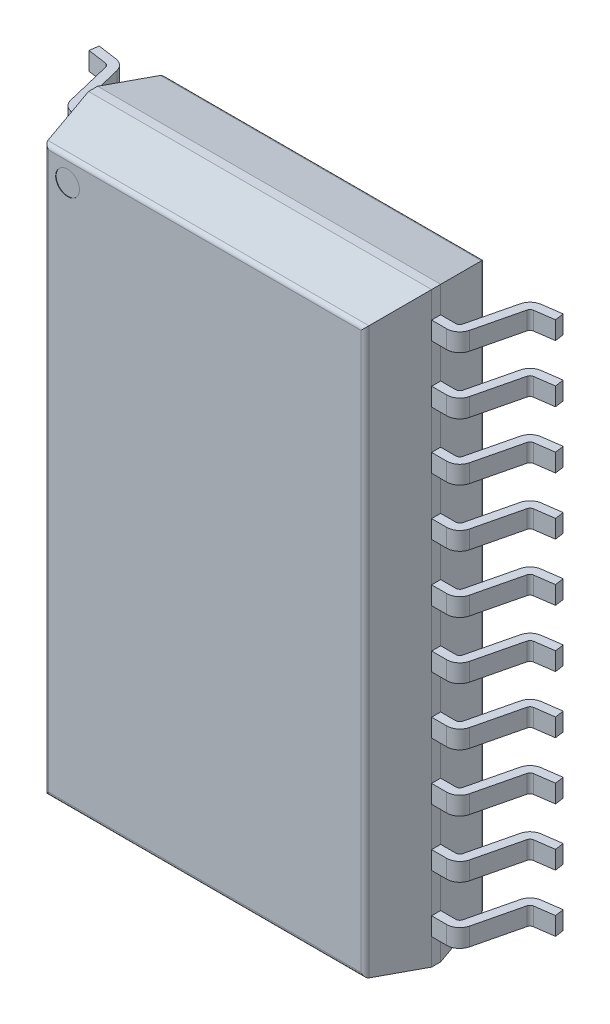
SolidWorks part; units mm, degrees
ref_plane "Front Plane" through (0, 0, 0) normal (0, 0, 1) x (1, 0, 0)
ref_plane "Top Plane" through (0, 0, 0) normal (0, 1, 0) x (1, 0, 0)
ref_plane "Right Plane" through (0, 0, 0) normal (1, 0, 0) x (0, 0, -1)
ref_plane "Body Standoff" through (0, 0.15, 0) normal (0, 1, 0) x (-1, 0, 0)
sketch "Sketch1" plane through (0, 0.15, 0) normal (0, 1, 0) x (-1, 0, 0)
  line L1 (3.8, 6.5) -> (-3.8, 6.5)
  line L2 (3.8, 6.5) -> (3.8, -6.5)
  line L3 (3.8, -6.5) -> (-3.8, -6.5)
  line L4 (-3.8, 6.5) -> (-3.8, -6.5)
  line L8 (0, 0) -> (0, -6.5) construction
  line L9 (0, 0) -> (-3.8, 0) construction
  dimension "D" = 13
  dimension "E1" = 7.6
extrude "Body" add sketch "Sketch1" along normal blind 2.65
chamfer "Body Chamfer" distance 1.225 angle 12 8 edges at (-3.8, 2.8, 0) (0, 0.15, 6.5) (3.8, 0.15, 0) (0, 0.15, -6.5) (-3.8, 0.15, 0) (0, 2.8, -6.5) (3.8, 2.8, 0) (0, 2.8, 6.5)
fillet "Fillet1" radius 0.1 8 edges at (0, 0.15, -6.2396) (-3.5396, 0.15, 0) (0, 0.15, 6.2396) (3.5396, 0.15, 0) (0, 2.8, 6.2396) (-3.5396, 2.8, 0) (0, 2.8, -6.2396) (3.5396, 2.8, 0)
sketch "Sketch2" plane through (0, 2.8, 0) normal (0, 1, 0) x (1, 0, 0)
  line L0 (3.5396, 6.2396) -> (-3.5396, 6.2396) construction
  line L1 (-3.5396, 6.2396) -> (-3.5396, -6.2396) construction
  circle A0 centre (-3.0396, 5.7396) radius 0.2635
  dimension "D1" = 0.5
  dimension "D2" = 0.5
extrude "Pin #1 Indent" cut sketch "Sketch2" against normal blind 0.01
ref_plane "Pin Offset" through (0, 0, 0.635) normal (0, 0, 1) x (1, 0, 0)
sketch "Sketch3" plane through (0, 0, 0.635) normal (0, 0, 1) x (1, 0, 0)
  line L0 (-5.14, 0) -> (-4.7116, 0.0602)
  line L2 (0, 0) -> (-5.14, 0) construction
  line L3 (-5.14, 0) -> (-5.1678, 0.1981)
  line L4 (-5.1678, 0.1981) -> (-4.7394, 0.2583)
  line L5 (-3.8, 1.575) -> (-3.8, 1.375)
  line L6 (-3.8, 1.375) -> (-4.135, 1.375)
  line L7 (-3.8, 1.575) -> (-4.135, 1.575)
  line L8 (-4.6644, 0.3263) -> (-4.4169, 1.353)
  line L9 (-4.2225, 1.3061) -> (-4.47, 0.2794)
  arc A0 (-4.7116, 0.0602) -> (-4.47, 0.2794) centre (-4.7519, 0.3474) ccw
  arc A1 (-4.7394, 0.2583) -> (-4.6644, 0.3263) centre (-4.7519, 0.3474) ccw
  arc A2 (-4.135, 1.575) -> (-4.4169, 1.353) centre (-4.135, 1.285) ccw
  arc A3 (-4.135, 1.375) -> (-4.2225, 1.3061) centre (-4.135, 1.285) ccw
  dimension "R" = 0.09
  dimension "θ1" = 8
  dimension "L" = 0.67
  dimension "S" = 0.335
  dimension "D1" = 1.34
  dimension "D2" = 0.2
extrude "Pin" add sketch "Sketch3" along normal blind 0.2 and the other way blind 0.2
pattern_linear "LPattern1" count 6 spacing 1.27 along (0, 0, -1) count 5 spacing 1.27 along (0, 0, 1) of "Pin"
mirror "Mirror1" about plane through (0, 0, 0) normal (1, 0, 0) of "LPattern1", "Pin"
move or copy body "Körper-Verschieben/Kopieren1" bodies to move or copy 108 copy no rotation origin (0, 0, 0) rotation axis (1, 0, 0) rotation angle 90
equation "\"D1@Body Chamfer\"=(\"D1@Body\"-\"D2@Sketch3\")/2"
